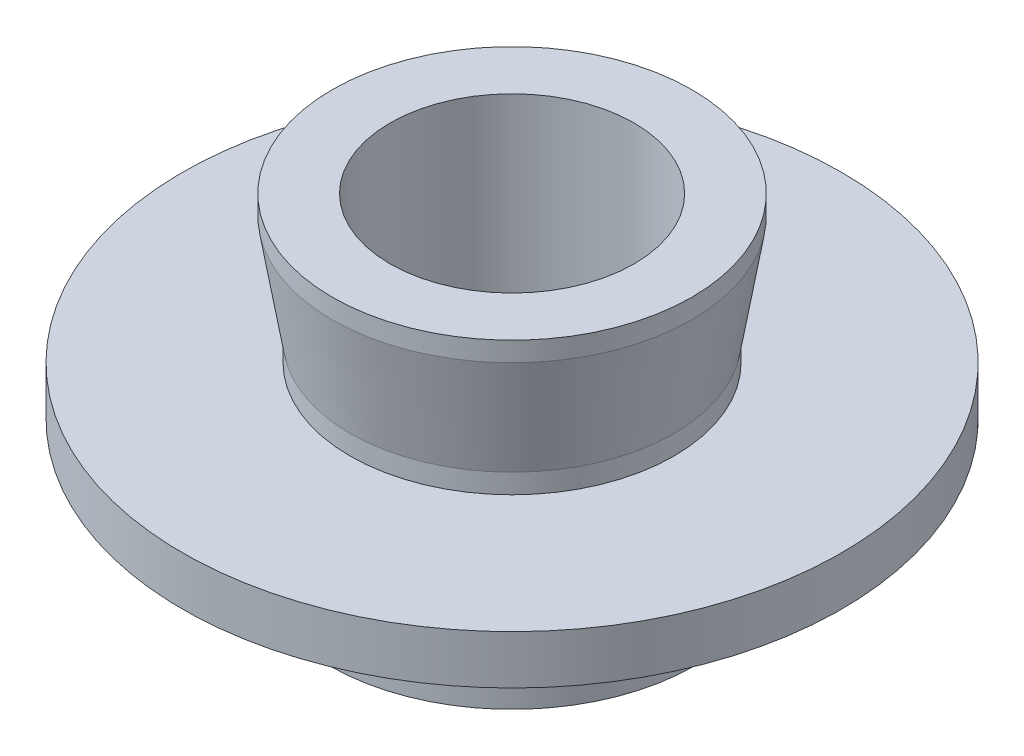
SolidWorks part; units mm, degrees
ref_plane "前视基准面" through (0, 0, 0) normal (0, 0, 1) x (1, 0, 0)
ref_plane "上视基准面" through (0, 0, 0) normal (0, 1, 0) x (1, 0, 0)
ref_plane "右视基准面" through (0, 0, 0) normal (1, 0, 0) x (0, 0, -1)
sketch "草图1" plane through (0, 0, 0) normal (0, 0, 1) x (1, 0, 0)
  line L0 (0, 0) -> (0, 73.2965) construction
  line L1 (-5, 0) -> (-5, 13)
  line L2 (-5, 13) -> (-7.365, 13)
  line L3 (-7.365, 13) -> (-7.365, 12.2)
  line L4 (-7.365, 12.2) -> (-6.635, 7.8)
  line L5 (-6.635, 7.8) -> (-6.635, 7)
  line L6 (-6.635, 7) -> (-13.5, 7)
  line L7 (-13.5, 7) -> (-13.5, 5)
  line L8 (-13.5, 5) -> (-7.1, 5)
  line L9 (-7.1, 5) -> (-7.1, 4)
  line L10 (-7.1, 4) -> (-7.5, 4)
  line L11 (-7.5, 4) -> (-7.5, 0)
  line L12 (-7.5, 0) -> (-5, 0)
  dimension "D1" = 5
  dimension "D2" = 7.365
  dimension "D3" = 6.635
  dimension "D4" = 7.5
  dimension "D5" = 7.1
  dimension "D6" = 13
  dimension "D7" = 6
  dimension "D8" = 2
  dimension "D9" = 1
  dimension "D10" = 0.8
  dimension "D11" = 0.8
  dimension "D12" = 0
  dimension "D13" = 13.5
revolve "旋转1" add sketch "草图1" angle 360 about L0
cosmetic thread "装饰螺纹线1" parameters "D1"=13, "D2"=11
cosmetic thread "装饰螺纹线2" parameters "D2"=14
